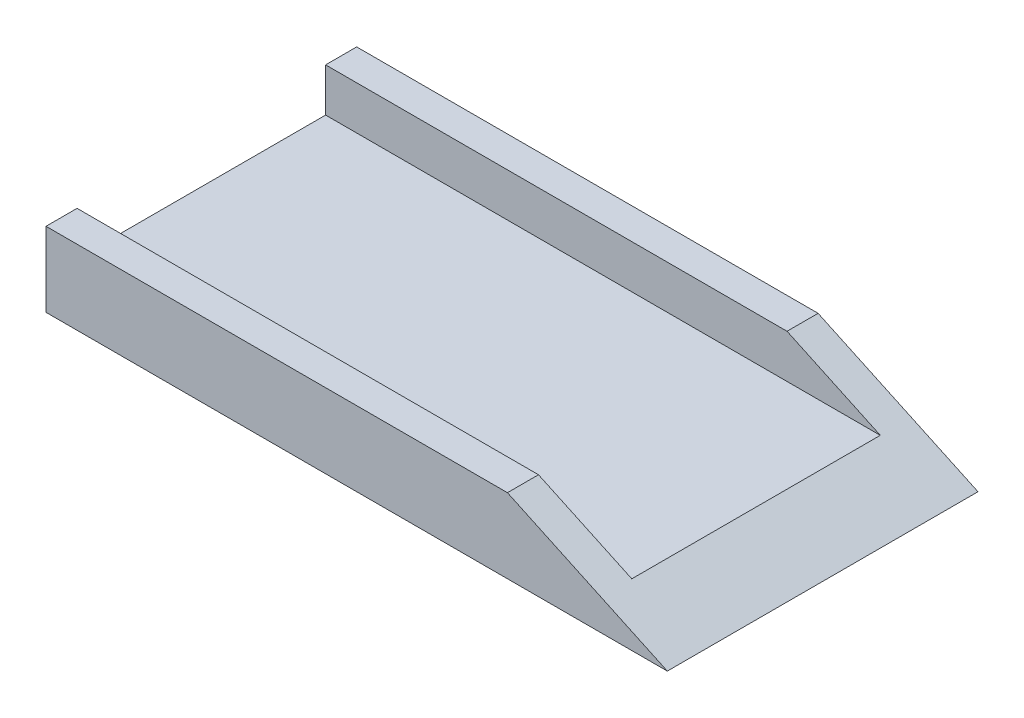
SolidWorks part; units mm, degrees
material "Maple"
ref_plane "Front Plane" through (0, 0, 0) normal (0, 0, 1) x (1, 0, 0)
ref_plane "Top Plane" through (0, 0, 0) normal (0, 1, 0) x (1, 0, 0)
ref_plane "Right Plane" through (0, 0, 0) normal (1, 0, 0) x (0, 0, -1)
sketch "Sketch1" plane through (0, 0, 0) normal (0, 0, 1) x (1, 0, 0)
  line L2 (-63.5, 3.175) -> (63.5, 3.175)
  line L3 (-63.5, 3.175) -> (-63.5, -3.175)
  line L4 (-63.5, -3.175) -> (63.5, -3.175)
  line L5 (63.5, 3.175) -> (63.5, -3.175)
  line L6 (-63.5, 3.175) -> (63.5, -3.175) construction
  line L7 (-63.5, -3.175) -> (63.5, 3.175) construction
  point P1 (0, 0)
  dimension "D1" = 6.35
  dimension "D2" = 127
extrude "Boss-Extrude1" add sketch "Sketch1" against normal blind 63.5
sketch "Sketch2" plane through (0, 3.175, 0) normal (0, 1, 0) x (1, 0, 0)
  line L1 (63.5, 63.5) -> (-63.5, 63.5)
  line L2 (63.5, 63.5) -> (63.5, 57.15)
  line L3 (63.5, 57.15) -> (-63.5, 57.15)
  line L4 (-63.5, 63.5) -> (-63.5, 57.15)
  line L5 (63.5, 63.5) -> (63.5, 0) construction
  line L6 (-63.5, 0) -> (63.5, 0)
  line L7 (-63.5, 0) -> (-63.5, 6.35)
  line L8 (-63.5, 6.35) -> (63.5, 6.35)
  line L9 (63.5, 0) -> (63.5, 6.35)
  line L10 (-63.5, 63.5) -> (-63.5, 0) construction
  line L11 (-63.5, 0) -> (63.5, 0) construction
  dimension "D1" = 6.35
  dimension "D2" = 6.35
extrude "Boss-Extrude2" add sketch "Sketch2" along normal blind 8.89
sketch "Sketch3" plane through (0, 0, 0) normal (0, 0, 1) x (1, 0, 0)
  line L0 (63.5, -3.175) -> (30.8177, 12.065)
  line L1 (-63.5, 12.065) -> (63.5, 12.065) construction
  line L2 (30.8177, 12.065) -> (41.5522, 35.0852)
  line L3 (41.5522, 35.0852) -> (74.2345, 19.8452)
  line L4 (74.2345, 19.8452) -> (63.5, -3.175)
  line L5 (-63.5, -3.175) -> (63.5, -3.175) construction
  dimension "D1" = 25
  dimension "D2" = 25.4
extrude "Cut-Extrude1" cut sketch "Sketch3" against normal through all
